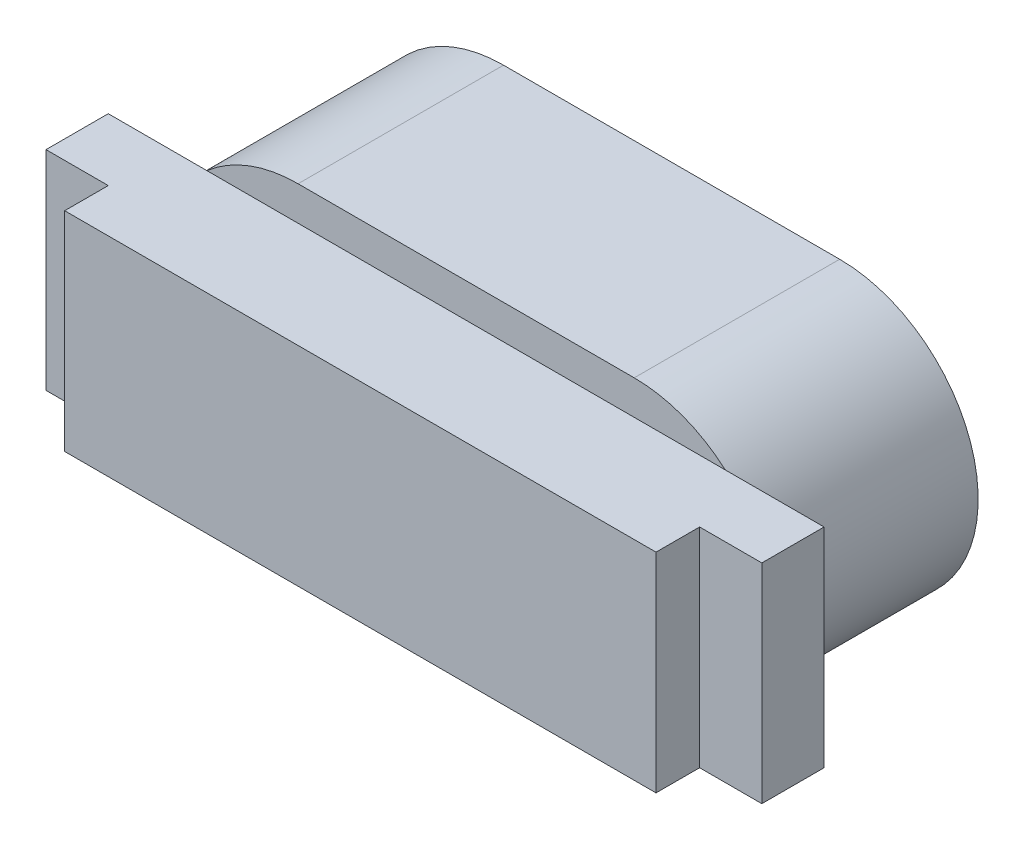
SolidWorks part; units mm, degrees
ref_plane "Plan de face" through (0, 0, 0) normal (0, 0, 1) x (1, 0, 0)
ref_plane "Plan de dessus" through (0, 0, 0) normal (0, 1, 0) x (1, 0, 0)
ref_plane "Plan de droite" through (0, 0, 0) normal (1, 0, 0) x (0, 0, -1)
sketch "Esquisse3" plane through (0, 0, 0) normal (0, 0, 1) x (1, 0, 0)
  line L0 (-2.7, 0) -> (2.7, 0) construction
  line L1 (-2.7, 2.225) -> (2.7, 2.225)
  line L2 (-2.7, -2.225) -> (2.7, -2.225)
  arc A0 (-2.7, 2.225) -> (-2.7, -2.225) centre (-2.7, 0) ccw
  arc A1 (2.7, -2.225) -> (2.7, 2.225) centre (2.7, 0) ccw
  point P2 (0, 0)
  dimension "D1" = 9.85
  dimension "D2" = 4.45
extrude "Boss.-Extru.1" add sketch "Esquisse3" along normal blind 3.3
sketch "Esquisse4" plane through (0, 0, 3.3) normal (0, 0, 1) x (1, 0, 0)
  line L1 (-5.75, 1.675) -> (5.75, 1.675)
  line L2 (-5.75, 1.675) -> (-5.75, -1.675)
  line L3 (-5.75, -1.675) -> (5.75, -1.675)
  line L4 (5.75, 1.675) -> (5.75, -1.675)
  line L5 (-5.75, 1.675) -> (5.75, -1.675) construction
  line L6 (-5.75, -1.675) -> (5.75, 1.675) construction
  point P0 (0, 0)
  dimension "D1" = 11.5
  dimension "D2" = 3.35
extrude "Boss.-Extru.2" add sketch "Esquisse4" along normal blind 1
sketch "Esquisse5" plane through (0, 0, 4.3) normal (0, 0, 1) x (1, 0, 0)
  line L0 (5.75, 1.675) -> (-5.75, 1.675) construction
  line L1 (-4.75, -1.675) -> (4.75, -1.675)
  line L2 (-4.75, -1.675) -> (-4.75, 1.675)
  line L3 (-4.75, 1.675) -> (4.75, 1.675)
  line L4 (4.75, -1.675) -> (4.75, 1.675)
  line L5 (-4.75, -1.675) -> (4.75, 1.675) construction
  line L6 (-4.75, 1.675) -> (4.75, -1.675) construction
  line L7 (-5.75, 1.675) -> (-5.75, -1.675) construction
  point P0 (0, 0)
  dimension "D1" = 1
extrude "Boss.-Extru.3" add sketch "Esquisse5" along normal blind 0.7
